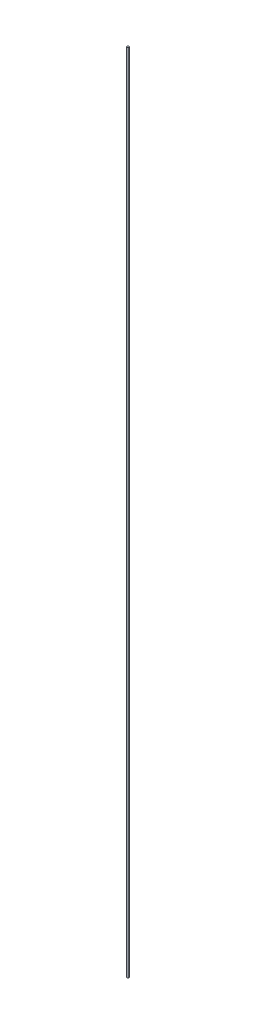
SolidWorks part; units mm, degrees
ref_plane "Front Plane" through (0, 0, 0) normal (0, 0, 1) x (1, 0, 0)
ref_plane "Top Plane" through (0, 0, 0) normal (0, 1, 0) x (1, 0, 0)
ref_plane "Right Plane" through (0, 0, 0) normal (1, 0, 0) x (0, 0, -1)
sketch "Sketch2" plane through (0, 0, 0) normal (0, 1, 0) x (1, 0, 0)
  circle A0 centre (0, 0) radius 1.016
  dimension "D1" = 2.032
extrude "Boss-Extrude1" add sketch "Sketch2" along normal blind 914.4
